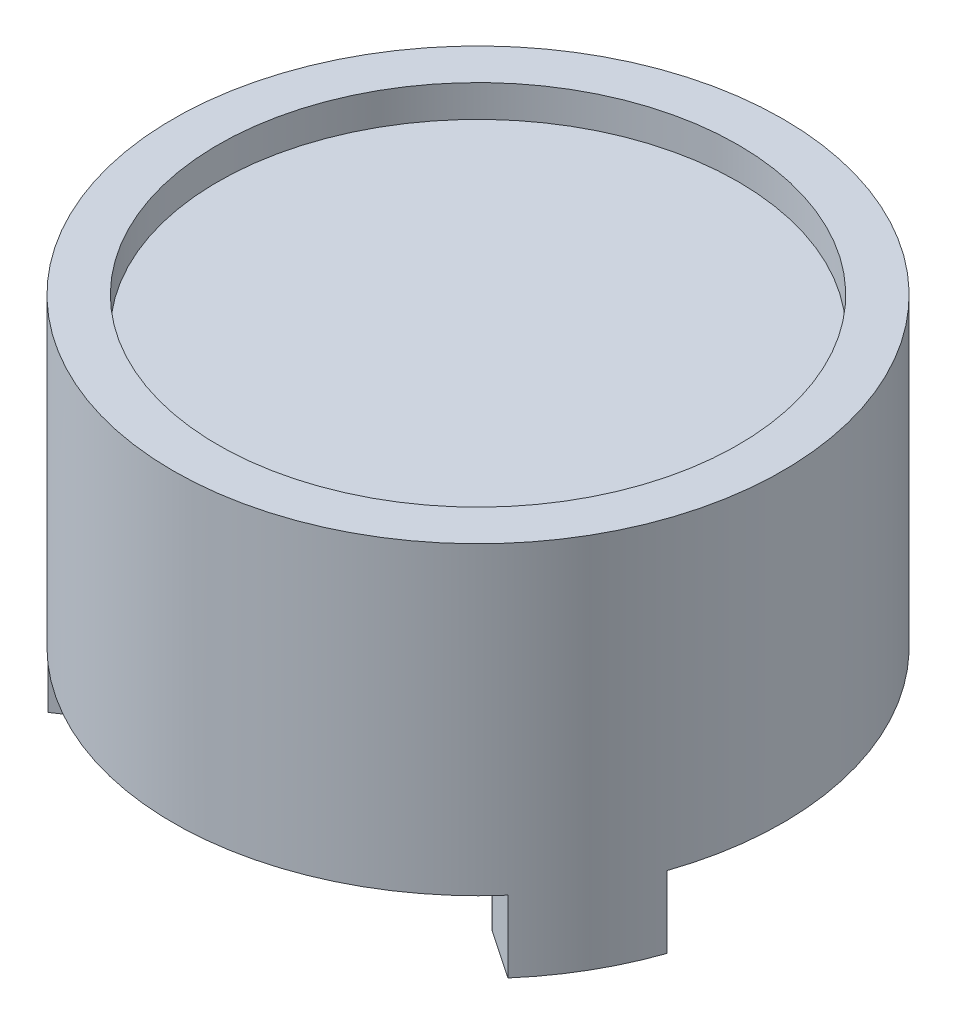
SolidWorks part; units mm, degrees
ref_plane "Front" through (0, 0, 0) normal (0, 0, 1) x (1, 0, 0)
ref_plane "Top" through (0, 0, 0) normal (0, 1, 0) x (1, 0, 0)
ref_plane "Right" through (0, 0, 0) normal (1, 0, 0) x (0, 0, -1)
sketch "Sketch4" plane through (0, 0, 0) normal (0, 0, 1) x (1, 0, 0)
  line L0 (0, 0) -> (0, 15.222) construction
  line L1 (0, 15.222) -> (14.5, 15.222)
  line L2 (13.5, 1) -> (13.5, 0)
  line L3 (13.5, 0) -> (17, 0)
  line L4 (17, 0) -> (17, 17)
  line L5 (17, 17) -> (14.5, 17)
  line L6 (14.5, 17) -> (14.5, 15.222)
  line L7 (14.5, 1) -> (13.5, 1)
  line L8 (14.5, 2.522) -> (0, 2.522)
  line L9 (0, 2.522) -> (0, 15.222)
  line L10 (14.5, 2.522) -> (14.5, 1)
  dimension "D1" = 34
  dimension "D2" = 2.5
  dimension "D3" = 27
  dimension "D4" = 1
  dimension "D5" = 17
  dimension "D6" = 12.7
  dimension "D7" = 1.778
revolve "Revolve1" add sketch "Sketch4" angle 360 about L0
sketch "Sketch3" plane through (0, 0, 0) normal (0, 1, 0) x (1, 0, 0)
  line L0 (-3.25, 16.6864) -> (-3, 13.1624)
  line L1 (3.25, 16.6864) -> (3, 13.1624)
  line L2 (0, 0) -> (0, 17) construction
  arc A0 (-3.25, 16.6864) -> (3.25, 16.6864) centre (0, 0) cw
  arc A3 (3, 13.1624) -> (-3, 13.1624) centre (0, 0) ccw
  circle A4 centre (0, 0) radius 13.5 construction
  circle A6 centre (0, 0) radius 17 construction
  circle A8 centre (0, 0) radius 13.5 construction
  dimension "D1" = 6
  dimension "D2" = 6.5
extrude "Tooth" add sketch "Sketch3" against normal blind 4
pattern_circular "Three Teeth" count 3 over 360 about axis through (0, 0, 0) along (0, 1, 0) of "Tooth"
fillet "Fillet1" radius 0.254 6 edges
